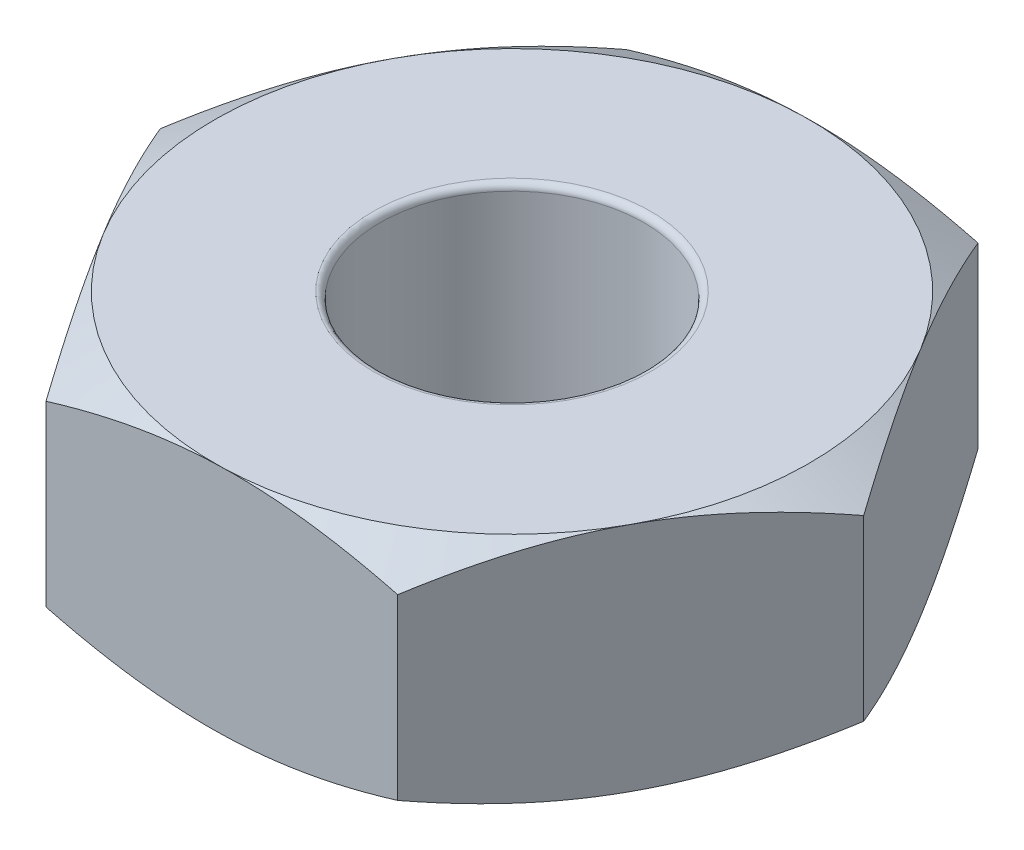
SolidWorks part; units mm, degrees
ref_plane "Front Plane" through (0, 0, 0) normal (0, 0, 1) x (1, 0, 0)
ref_plane "Top Plane" through (0, 0, 0) normal (0, 1, 0) x (1, 0, 0)
ref_plane "Right Plane" through (0, 0, 0) normal (1, 0, 0) x (0, 0, -1)
sketch "Sketch1" plane through (0, 0, 0) normal (0, 1, 0) x (1, 0, 0)
  line L1 (1.3532, -2.2179) -> (2.5973, 0.0629)
  line L2 (2.5973, 0.0629) -> (1.2441, 2.2808)
  line L3 (1.2441, 2.2808) -> (-1.3532, 2.2179)
  line L4 (-1.3532, 2.2179) -> (-2.5973, -0.0629)
  line L5 (-2.5973, -0.0629) -> (-1.2441, -2.2808)
  line L6 (-1.2441, -2.2808) -> (1.3532, -2.2179)
  circle A0 centre (0, 0) radius 1
  circle A1 centre (0, 0) radius 2.25 construction
  dimension "D1" = 2
  dimension "D2" = 4.5
extrude "Boss-Extrude1" add sketch "Sketch1" along normal blind 1.75
sketch "Sketch2" plane through (0, 1.75, 0) normal (0, 1, 0) x (1, 0, 0)
sketch "Sketch3" plane through (0, 1.75, 0) normal (0, 1, 0) x (1, 0, 0)
  circle A0 centre (0, 0) radius 2.25 construction
  circle A1 centre (0, 0) radius 2.25
extrude "Cut-Extrude2" cut sketch "Sketch3" against normal blind 1.75 draft 60 flip side to cut
sketch "Sketch4" plane through (0, 0, 0) normal (0, -1, 0) x (1, 0, 0)
  circle A0 centre (0, 0) radius 2.25 construction
  circle A1 centre (0, 0) radius 2.25
extrude "Cut-Extrude3" cut sketch "Sketch4" against normal blind 1.75 draft 60 flip side to cut
fillet "Fillet1" radius 0.05 2 edges at (0, 1.75, 1) (0, 0, 1)
